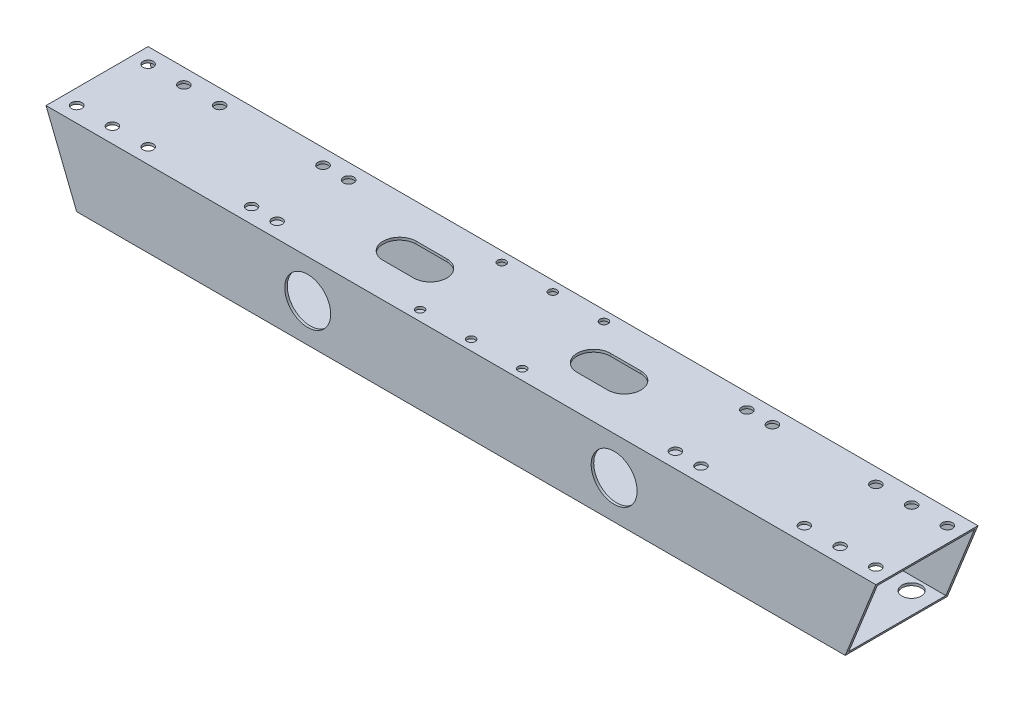
SolidWorks part; units mm, degrees
material "6061-T6 (SS)"
ref_plane "前视基准面" through (0, 0, 0) normal (0, 0, 1) x (1, 0, 0)
ref_plane "上视基准面" through (0, 0, 0) normal (0, 1, 0) x (1, 0, 0)
ref_plane "右视基准面" through (0, 0, 0) normal (1, 0, 0) x (0, 0, -1)
sketch "草图1" plane through (0, 0, 0) normal (1, 0, 0) x (0, 0, -1)
  line L0 (-19, 14) -> (-19, -14)
  line L1 (-20, 15) -> (20, 15)
  line L2 (-20, 15) -> (-20, -15)
  line L3 (-20, -15) -> (20, -15)
  line L4 (20, 15) -> (20, -15)
  line L5 (0, -15) -> (0, 15) construction
  line L6 (-20, 0) -> (20, 0) construction
  line L7 (-19, -14) -> (19, -14)
  line L8 (19, 14) -> (19, -14)
  line L9 (-19, 14) -> (19, 14)
  point P0 (0, 0)
  dimension "D1" = 30
  dimension "40" = 40
  dimension "D2" = 1
extrude "凸台-拉伸1" add sketch "草图1" along normal blind 325
sketch "草图2" plane through (0, -15, 0) normal (0, -1, 0) x (1, 0, 0)
  line L0 (162.5, 20) -> (162.5, -49980) construction
  line L1 (325, 20) -> (0, 20) construction
  line L2 (0, 0) -> (50000, 0) construction
  line L3 (250.5, 0) -> (240.5, 0) construction
  line L4 (74.5, 14) -> (84.5, 14) construction
  line L5 (74.5, 14) -> (74.5, -14) construction
  line L6 (74.5, -14) -> (84.5, -14) construction
  line L7 (84.5, 14) -> (84.5, -14) construction
  line L8 (79.5, -14) -> (79.5, 14) construction
  line L9 (74.5, 0) -> (84.5, 0) construction
  line L10 (245.5, -14) -> (245.5, 14) construction
  line L11 (240.5, 14) -> (240.5, -14) construction
  line L12 (250.5, -14) -> (240.5, -14) construction
  line L13 (250.5, 14) -> (250.5, -14) construction
  line L14 (250.5, 14) -> (240.5, 14) construction
  circle A0 centre (74.5, 14) radius 2.025
  circle A1 centre (84.5, 14) radius 2.025
  circle A2 centre (84.5, -14) radius 2.025
  circle A3 centre (74.5, -14) radius 2.025
  circle A4 centre (250.5, -14) radius 2.025
  circle A5 centre (240.5, -14) radius 2.025
  circle A6 centre (240.5, 14) radius 2.025
  circle A7 centre (250.5, 14) radius 2.025
  point P4 (162.5, 20)
  point P8 (79.5, 0)
  point P29 (245.5, 0)
  dimension "D2" = 4.05
  dimension "D1" = 10
  dimension "28" = 28
  dimension "83" = 83
extrude "切除-拉伸1" cut sketch "草图2" against normal through all
sketch "草图3" plane through (0, -15, 0) normal (0, -1, 0) x (1, 0, 0)
  line L0 (162.5, -20) -> (162.5, -50020) construction
  line L1 (325, -20) -> (0, -20) construction
  line L2 (0, 0) -> (50000, 0) construction
  line L3 (0, 20) -> (0, -20) construction
  line L4 (18.6091, 0) -> (50018.6091, 0) construction
  line L5 (325, 20) -> (325, -20) construction
  line L6 (291, 14) -> (319, 14) construction
  line L7 (291, 14) -> (291, -14) construction
  line L8 (291, -14) -> (319, -14) construction
  line L9 (319, 14) -> (319, -14) construction
  line L10 (305, -14) -> (305, 14) construction
  line L11 (291, 0) -> (319, 0) construction
  line L12 (291, -14) -> (319, -14) construction
  line L13 (34, -14) -> (6, -14) construction
  line L14 (34, 0) -> (6, 0) construction
  line L15 (20, -14) -> (20, 14) construction
  line L16 (6, 14) -> (6, -14) construction
  line L17 (34, -14) -> (6, -14) construction
  line L18 (34, 14) -> (34, -14) construction
  line L19 (34, 14) -> (6, 14) construction
  circle A0 centre (291, 14) radius 2.025
  circle A1 centre (305, 14) radius 2.025
  circle A2 centre (319, 14) radius 2.025
  circle A3 centre (319, -14) radius 2.025
  circle A4 centre (305, -14) radius 2.025
  circle A5 centre (291, -14) radius 2.025
  circle A6 centre (34, -14) radius 2.025
  circle A7 centre (20, -14) radius 2.025
  circle A8 centre (6, -14) radius 2.025
  circle A9 centre (6, 14) radius 2.025
  circle A10 centre (20, 14) radius 2.025
  circle A11 centre (34, 14) radius 2.025
  point P4 (162.5, -20)
  point P9 (0, 0)
  point P12 (305, 0)
  point P39 (20, 0)
  dimension "D3" = 4.05
  dimension "D1" = 28
  dimension "D2" = 20
  dimension "20" = 28
extrude "切除-拉伸2" cut sketch "草图3" against normal through all
sketch "草图4" plane through (0, -15, 0) normal (0, -1, 0) x (1, 0, 0)
  line L0 (162.5, 20) -> (162.5, -49980) construction
  line L1 (325, 20) -> (0, 20) construction
  line L2 (0, 0) -> (50000, 0) construction
  line L3 (142.5, 16) -> (162.5, 16) construction
  line L4 (142.5, -16) -> (162.5, -16) construction
  circle A0 centre (142.5, 16) radius 1.6
  circle A1 centre (162.5, 16) radius 1.6
  circle A2 centre (182.5, 16) radius 1.6
  circle A3 centre (182.5, -16) radius 1.6
  circle A4 centre (162.5, -16) radius 1.6
  circle A5 centre (142.5, -16) radius 1.6
  point P4 (162.5, 20)
  dimension "D1" = 3.2
  dimension "D2" = 32
  dimension "D3" = 20
  dimension "D5" = 20
  dimension "D4" = 3
extrude "切除-拉伸3" cut sketch "草图4" against normal through all
sketch "草图5" plane through (0, 0, 20) normal (0, 0, 1) x (1, 0, 0)
  line L0 (162.5, 15) -> (162.5, -49985) construction
  line L1 (325, 15) -> (0, 15) construction
  line L2 (0, 15) -> (12, -15)
  line L3 (325, -15) -> (0, -15) construction
  line L4 (12, -15) -> (0, -15)
  line L5 (0, -15) -> (0, 15)
  line L6 (313, -15) -> (325, -15)
  line L7 (325, 15) -> (313, -15)
  line L8 (325, -15) -> (325, 15)
  point P4 (162.5, 15)
  dimension "D1" = 12
extrude "切除-拉伸4" cut sketch "草图5" against normal through all
sketch "草图6" plane through (0, -15, 0) normal (0, -1, 0) x (1, 0, 0)
  line L0 (162.5, 20) -> (162.5, -49980) construction
  line L1 (313, 20) -> (12, 20) construction
  line L2 (250.5, 0) -> (240.5, 0) construction
  line L3 (74.5, 14) -> (84.5, 14) construction
  line L4 (74.5, 14) -> (74.5, -14) construction
  line L5 (74.5, -14) -> (84.5, -14) construction
  line L6 (84.5, 14) -> (84.5, -14) construction
  line L7 (79.5, -14) -> (79.5, 14) construction
  line L8 (74.5, 0) -> (84.5, 0) construction
  line L9 (245.5, -14) -> (245.5, 14) construction
  line L10 (240.5, 14) -> (240.5, -14) construction
  line L11 (250.5, -14) -> (240.5, -14) construction
  line L12 (250.5, 14) -> (250.5, -14) construction
  line L13 (250.5, 14) -> (240.5, 14) construction
  circle A0 centre (74.5, 14) radius 3.75
  circle A1 centre (84.5, 14) radius 3.75
  circle A2 centre (84.5, -14) radius 3.75
  circle A3 centre (74.5, -14) radius 3.75
  circle A4 centre (250.5, -14) radius 3.75
  circle A5 centre (240.5, -14) radius 3.75
  circle A6 centre (240.5, 14) radius 3.75
  circle A7 centre (250.5, 14) radius 3.75
  point P4 (162.5, 20)
  point P25 (245.5, 0)
  point P101 (79.5, 0)
  dimension "D1" = 7.5
extrude "切除-拉伸5" cut sketch "草图6" against normal up to next
sketch "草图7" plane through (0, -15, 0) normal (0, -1, 0) x (1, 0, 0)
  line L0 (162.5, 20) -> (162.5, -49980) construction
  line L1 (20, 14) -> (34, 14) construction
  line L2 (20, 14) -> (20, -14) construction
  line L3 (20, -14) -> (34, -14) construction
  line L4 (34, 14) -> (34, -14) construction
  line L5 (27, -14) -> (27, 14) construction
  line L6 (20, 0) -> (34, 0) construction
  line L7 (313, 20) -> (12, 20) construction
  line L8 (305, 0) -> (291, 0) construction
  line L9 (298, -14) -> (298, 14) construction
  line L10 (291, 14) -> (291, -14) construction
  line L11 (305, -14) -> (291, -14) construction
  line L12 (305, 14) -> (305, -14) construction
  line L13 (305, 14) -> (291, 14) construction
  circle A0 centre (20, 14) radius 3.75
  circle A1 centre (34, 14) radius 3.75
  circle A2 centre (34, -14) radius 3.75
  circle A3 centre (20, -14) radius 3.75
  circle A4 centre (305, -14) radius 3.75
  circle A5 centre (291, -14) radius 3.75
  circle A6 centre (291, 14) radius 3.75
  circle A7 centre (305, 14) radius 3.75
  point P12 (162.5, 20)
  point P25 (298, 0)
  point P92 (27, 0)
  dimension "D1" = 7.5
extrude "切除-拉伸6" cut sketch "草图7" against normal up to next
sketch "草图8" plane through (0, 0, 20) normal (0, 0, 1) x (1, 0, 0)
  line L0 (162.5, 15) -> (162.5, -15) construction
  line L1 (325, 15) -> (0, 15) construction
  line L2 (313, -15) -> (12, -15) construction
  line L3 (162.5, 0) -> (-49837.5, 0) construction
  circle A0 centre (102.5, 0) radius 9
  circle A1 centre (222.5, 0) radius 9
  point P8 (162.5, 0)
  dimension "D1" = 18
  dimension "D2" = 60
extrude "切除-拉伸7" cut sketch "草图8" against normal up to next
sketch "草图9" plane through (0, 15, 0) normal (0, 1, 0) x (1, 0, 0)
  line L0 (162.5, 20) -> (162.5, -20) construction
  line L1 (325, 20) -> (0, 20) construction
  line L2 (325, -20) -> (0, -20) construction
  line L3 (162.5, 0) -> (50162.5, 0) construction
  line L4 (118.5, 0) -> (130.5, 0) construction
  line L5 (118.5, 6.5) -> (130.5, 6.5)
  line L6 (118.5, -6.5) -> (130.5, -6.5)
  line L7 (206.5, 0) -> (194.5, 0) construction
  line L8 (206.5, 6.5) -> (194.5, 6.5)
  line L9 (206.5, -6.5) -> (194.5, -6.5)
  arc A1 (118.5, 6.5) -> (118.5, -6.5) centre (118.5, 0) ccw
  arc A2 (130.5, -6.5) -> (130.5, 6.5) centre (130.5, 0) ccw
  arc A3 (206.5, 6.5) -> (206.5, -6.5) centre (206.5, 0) cw
  arc A4 (194.5, -6.5) -> (194.5, 6.5) centre (194.5, 0) cw
  point P8 (162.5, 0)
  point P11 (124.5, 0)
  point P19 (200.5, 0)
  dimension "D1" = 6.5
  dimension "D2" = 12
  dimension "35" = 38
extrude "切除-拉伸8" cut sketch "草图9" against normal up to next
